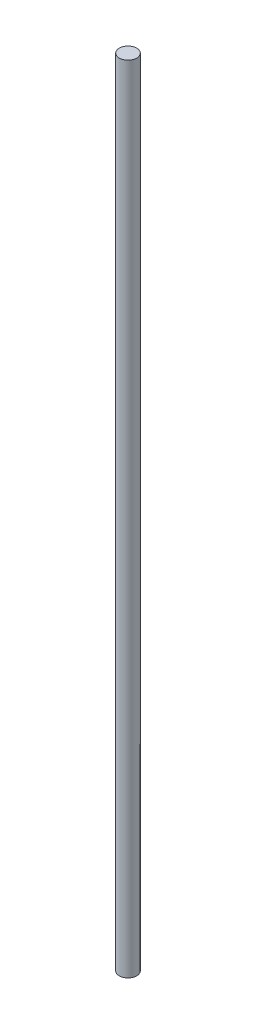
SolidWorks part; units mm, degrees
ref_plane "Front Plane" through (0, 0, 0) normal (0, 0, 1) x (1, 0, 0)
ref_plane "Top Plane" through (0, 0, 0) normal (0, 1, 0) x (1, 0, 0)
ref_plane "Right Plane" through (0, 0, 0) normal (1, 0, 0) x (0, 0, -1)
sketch "Sketch2" plane through (0, 0, 0) normal (0, 1, 0) x (1, 0, 0)
  circle A0 centre (0, 0) radius 0.875
  dimension "D1" = 1.75
extrude "Boss-Extrude1" add sketch "Sketch2" along normal blind 80
